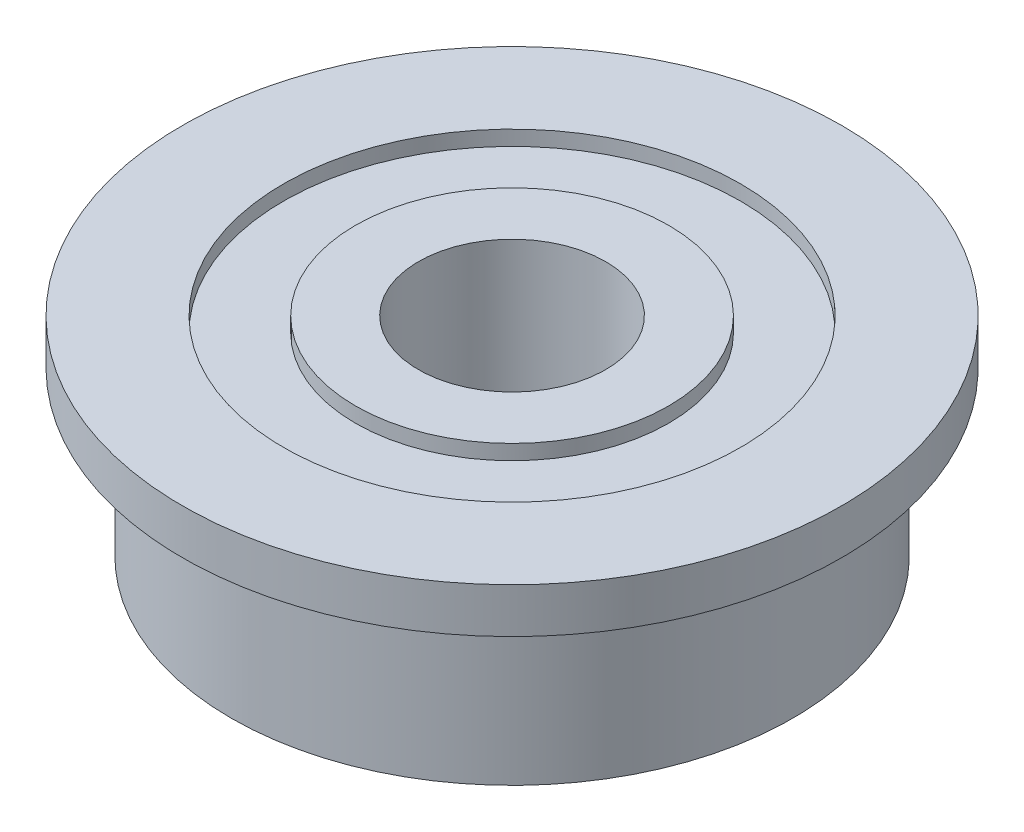
SolidWorks part; units mm, degrees
ref_plane "Front Plane" through (0, 0, 0) normal (0, 0, 1) x (1, 0, 0)
ref_plane "Top Plane" through (0, 0, 0) normal (0, 1, 0) x (1, 0, 0)
ref_plane "Right Plane" through (0, 0, 0) normal (1, 0, 0) x (0, 0, -1)
sketch "Sketch1" plane through (0, 0, 0) normal (0, 0, 1) x (1, 0, 0)
  line L0 (2.6543, 0) -> (2.6543, 0.254)
  line L1 (2.6543, 0.254) -> (3.8735, 0.254)
  line L2 (3.8735, 0.254) -> (3.8735, 0)
  line L3 (3.8735, 0) -> (4.7625, 0)
  line L4 (4.7625, 0) -> (4.7625, 2.7686)
  line L5 (4.7625, 2.7686) -> (5.588, 2.7686)
  line L6 (5.588, 2.7686) -> (5.588, 3.5306)
  line L7 (5.588, 3.5306) -> (3.8735, 3.5306)
  line L8 (3.8735, 3.5306) -> (3.8735, 3.2766)
  line L9 (3.8735, 3.2766) -> (2.6543, 3.2766)
  line L10 (2.6543, 3.2766) -> (2.6543, 3.5306)
  line L11 (2.6543, 3.5306) -> (1.5875, 3.5306)
  line L12 (1.5875, 3.5306) -> (1.5875, 0)
  line L13 (1.5875, 0) -> (2.6543, 0)
  line L14 (0, 3.5306) -> (0, 0) construction
revolve "Revolve1" add sketch "Sketch1" angle 360 about L14
